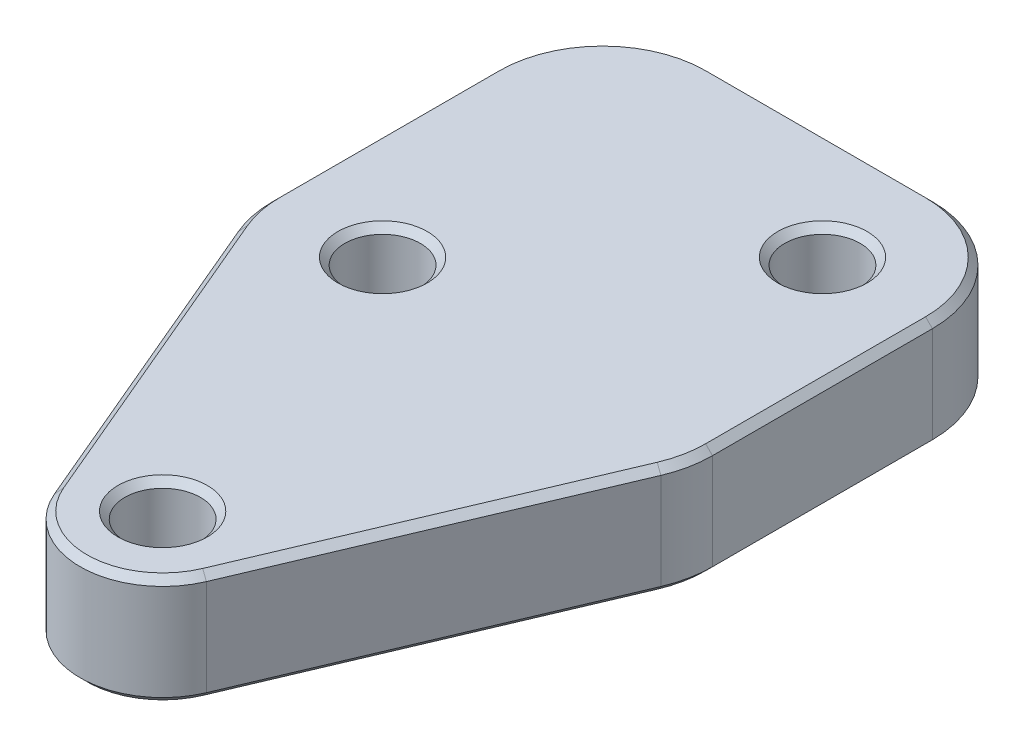
SolidWorks part; units mm, degrees
ref_plane "Front Plane" through (0, 0, 0) normal (0, 0, 1) x (1, 0, 0)
ref_plane "Top Plane" through (0, 0, 0) normal (0, 1, 0) x (1, 0, 0)
ref_plane "Right Plane" through (0, 0, 0) normal (1, 0, 0) x (0, 0, -1)
sketch "Sketch1" plane through (0, 0, 0) normal (0, 1, 0) x (1, 0, 0)
  line L0 (-12.7, 19.05) -> (-12.7, 31.75)
  line L1 (12.7, 19.05) -> (12.7, 31.75)
  line L2 (-6.35, 38.1) -> (6.35, 38.1)
  line L3 (-12.1965, 16.572) -> (-4.3849, -1.8585)
  line L4 (4.3849, -1.8585) -> (12.1965, 16.572)
  arc A0 (-4.3849, -1.8585) -> (4.3849, -1.8585) centre (0, 0) ccw
  circle A1 centre (0, 0) radius 2.1828
  circle A2 centre (6.35, 31.75) radius 2.1828
  circle A3 centre (-6.35, 19.05) radius 2.1828
  arc A4 (-12.7, 19.05) -> (-12.1965, 16.572) centre (-6.35, 19.05) ccw
  arc A5 (12.1965, 16.572) -> (12.7, 19.05) centre (6.35, 19.05) ccw
  arc A6 (12.7, 31.75) -> (6.35, 38.1) centre (6.35, 31.75) ccw
  arc A7 (-12.7, 31.75) -> (-6.35, 38.1) centre (-6.35, 31.75) cw
  dimension "D1" = 9.525
  dimension "D2" = 4.3656
  dimension "D3" = 4.3656
  dimension "D4" = 4.3656
  dimension "D9" = 12.7
  dimension "D10" = 12.7
  dimension "D12" = 6.35
  dimension "D5" = 19.05
  dimension "D6" = 6.35
  dimension "D7" = 6.35
  dimension "D8" = 12.7
  dimension "D11" = 6.35
extrude "Boss-Extrude1" add sketch "Sketch1" along normal blind 6.35
chamfer "Chamfer1" distance 0.3969 angle 45 26 edges at (-6.35, 0, -16.8672) (6.35, 0, -29.5672) (0, 0, 2.1828) (12.7, 0, -25.4) (10.8401, 0, -36.2401) (0, 0, -38.1) (-10.8401, 0, -36.2401) (-12.7, 0, -25.4) (-12.5729, 0, -17.7857) (-8.2907, 0, -7.3567) (0, 0, 4.7625) (8.2907, 0, -7.3567) (12.5729, 0, -17.7857) (-6.35, 6.35, -16.8672) (0, 6.35, 2.1828) (8.2907, 6.35, -7.3567) (0, 6.35, 4.7625) (-8.2907, 6.35, -7.3567) (-12.5729, 6.35, -17.7857) (-12.7, 6.35, -25.4) (-10.8401, 6.35, -36.2401) (0, 6.35, -38.1) (10.8401, 6.35, -36.2401) (12.7, 6.35, -25.4) (12.5729, 6.35, -17.7857) (6.35, 6.35, -29.5672)
